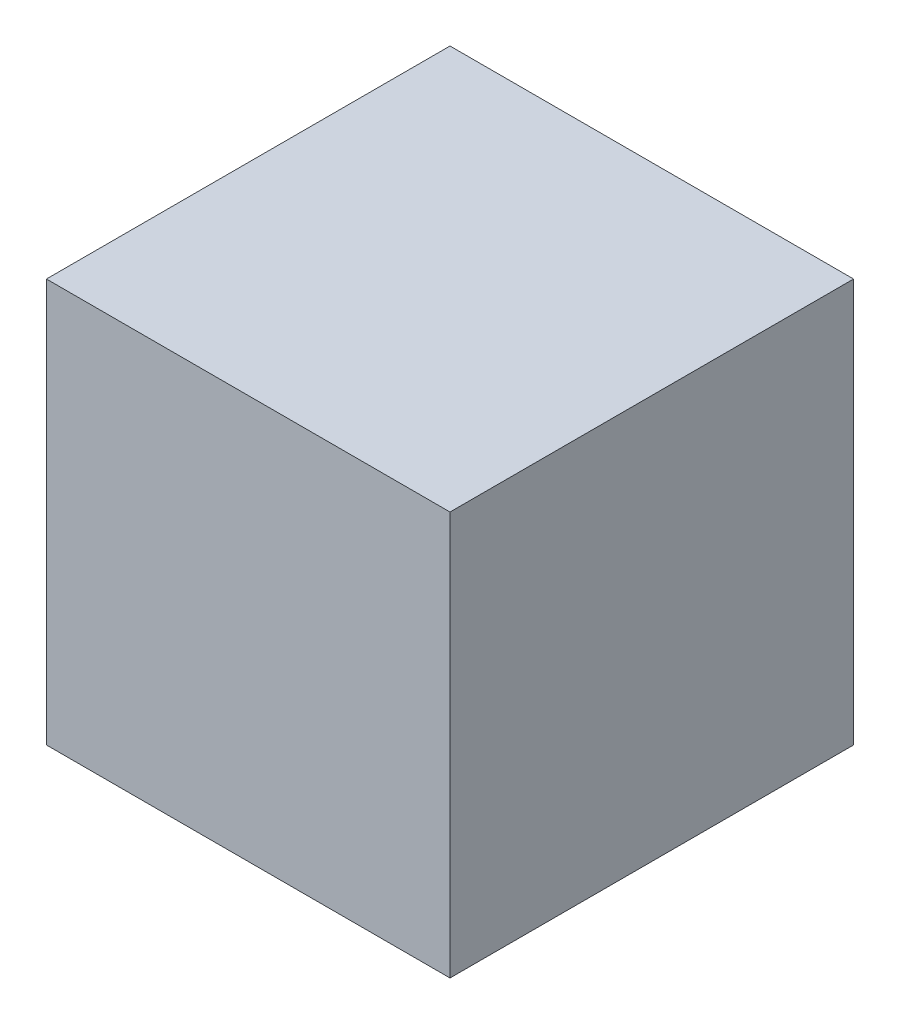
SolidWorks part; units mm, degrees
ref_plane "Front Plane" through (0, 0, 0) normal (0, 0, 1) x (1, 0, 0)
ref_plane "Top Plane" through (0, 0, 0) normal (0, 1, 0) x (1, 0, 0)
ref_plane "Right Plane" through (0, 0, 0) normal (1, 0, 0) x (0, 0, -1)
sketch "Sketch1" plane through (0, 0, 0) normal (0, 0, 1) x (1, 0, 0)
  line L1 (0, 0) -> (-10, 0)
  line L2 (0, 0) -> (0, 10)
  line L3 (0, 10) -> (-10, 10)
  line L4 (-10, 0) -> (-10, 10)
  dimension "D1" = 10
  dimension "D2" = 10
extrude "Boss-Extrude1" add sketch "Sketch1" along normal blind 10
